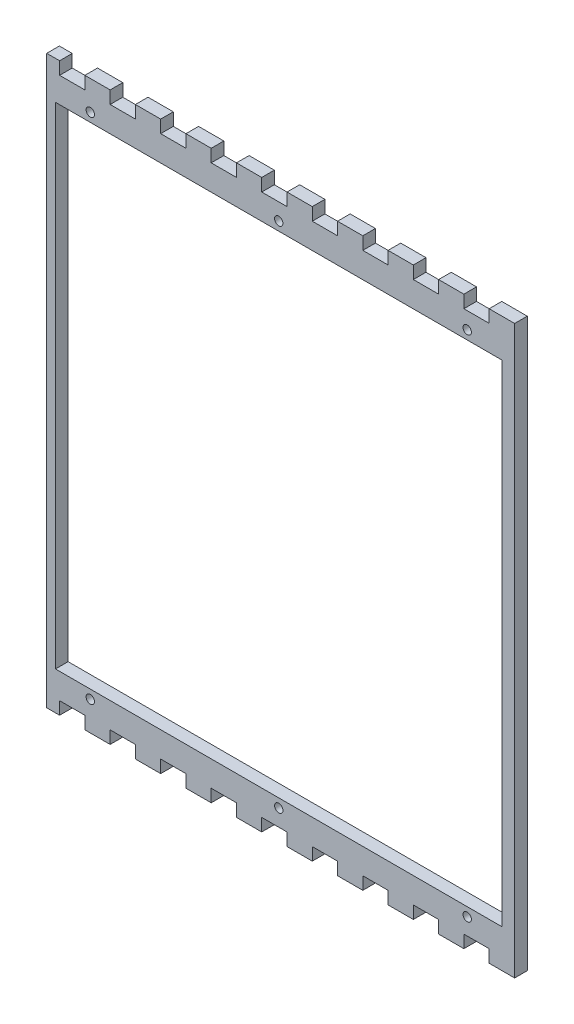
SolidWorks part; units mm, degrees
ref_plane "Front Plane" through (0, 0, 0) normal (0, 0, 1) x (1, 0, 0)
ref_plane "Top Plane" through (0, 0, 0) normal (0, 1, 0) x (1, 0, 0)
ref_plane "Right Plane" through (0, 0, 0) normal (1, 0, 0) x (0, 0, -1)
sketch "Model" plane through (0, 0, 0) normal (0, 0, 1) x (1, 0, 0)
  line L667 (1024.0797, 23.2006) -> (1029.904, 23.2006)
  line L668 (1029.904, 23.2006) -> (1029.904, 28.9154)
  line L669 (1029.904, 28.9154) -> (1041.334, 28.9154)
  line L670 (1041.334, 28.9154) -> (1041.334, 23.2006)
  line L671 (1041.334, 23.2006) -> (1052.764, 23.2006)
  line L672 (1052.764, 23.2006) -> (1052.764, 28.9154)
  line L673 (1052.764, 28.9154) -> (1064.194, 28.9154)
  line L674 (1064.194, 28.9154) -> (1064.194, 23.2006)
  line L675 (1064.194, 23.2006) -> (1075.624, 23.2006)
  line L676 (1075.624, 23.2006) -> (1075.624, 28.9154)
  line L677 (1075.624, 28.9154) -> (1087.054, 28.9154)
  line L678 (1087.054, 28.9154) -> (1087.054, 23.2006)
  line L679 (1087.054, 23.2006) -> (1098.484, 23.2006)
  line L680 (1098.484, 23.2006) -> (1098.484, 28.9154)
  line L681 (1098.484, 28.9154) -> (1109.914, 28.9154)
  line L682 (1109.914, 28.9154) -> (1109.914, 23.2006)
  line L683 (1109.914, 23.2006) -> (1121.344, 23.2006)
  line L684 (1121.344, 23.2006) -> (1121.344, 28.9154)
  line L685 (1121.344, 28.9154) -> (1132.774, 28.9154)
  line L686 (1132.774, 28.9154) -> (1132.774, 23.2006)
  line L687 (1132.774, 23.2006) -> (1144.204, 23.2006)
  line L688 (1144.204, 23.2006) -> (1144.204, 28.9154)
  line L689 (1144.204, 28.9154) -> (1155.634, 28.9154)
  line L690 (1155.634, 28.9154) -> (1155.634, 23.2006)
  line L691 (1155.634, 23.2006) -> (1167.064, 23.2006)
  line L692 (1167.064, 23.2006) -> (1167.064, 28.9154)
  line L693 (1167.064, 28.9154) -> (1178.494, 28.9154)
  line L694 (1178.494, 28.9154) -> (1178.494, 23.2006)
  line L695 (1178.494, 23.2006) -> (1189.924, 23.2006)
  line L696 (1189.924, 23.2006) -> (1189.924, 28.9154)
  line L697 (1189.924, 28.9154) -> (1201.354, 28.9154)
  line L698 (1201.354, 28.9154) -> (1201.354, 23.2006)
  line L699 (1201.354, 23.2006) -> (1212.784, 23.2006)
  line L700 (1212.784, 23.2006) -> (1212.784, 28.9154)
  line L701 (1212.784, 28.9154) -> (1224.214, 28.9154)
  line L702 (1224.214, 28.9154) -> (1224.214, 23.2006)
  line L703 (1224.214, 23.2006) -> (1235.7532, 23.2006)
  line L704 (1235.7532, 23.2006) -> (1235.7532, 279.6311)
  line L705 (1235.7532, 279.6311) -> (1224.214, 279.6311)
  line L706 (1224.214, 279.6311) -> (1224.214, 273.9161)
  line L707 (1224.214, 273.9161) -> (1212.784, 273.9161)
  line L708 (1212.784, 273.9161) -> (1212.784, 279.6311)
  line L709 (1212.784, 279.6311) -> (1201.354, 279.6311)
  line L710 (1201.354, 279.6311) -> (1201.354, 273.9161)
  line L711 (1201.354, 273.9161) -> (1189.924, 273.9161)
  line L712 (1189.924, 273.9161) -> (1189.924, 279.6311)
  line L713 (1189.924, 279.6311) -> (1178.494, 279.6311)
  line L714 (1178.494, 279.6311) -> (1178.494, 273.9161)
  line L715 (1178.494, 273.9161) -> (1167.064, 273.9161)
  line L716 (1167.064, 273.9161) -> (1167.064, 279.6311)
  line L717 (1167.064, 279.6311) -> (1155.634, 279.6311)
  line L718 (1155.634, 279.6311) -> (1155.634, 273.9161)
  line L719 (1155.634, 273.9161) -> (1144.204, 273.9161)
  line L720 (1144.204, 273.9161) -> (1144.204, 279.6311)
  line L721 (1144.204, 279.6311) -> (1132.774, 279.6311)
  line L722 (1132.774, 279.6311) -> (1132.774, 273.9161)
  line L723 (1132.774, 273.9161) -> (1121.344, 273.9161)
  line L724 (1121.344, 273.9161) -> (1121.344, 279.6311)
  line L725 (1121.344, 279.6311) -> (1109.914, 279.6311)
  line L726 (1109.914, 279.6311) -> (1109.914, 273.9161)
  line L727 (1109.914, 273.9161) -> (1098.484, 273.9161)
  line L728 (1098.484, 273.9161) -> (1098.484, 279.6311)
  line L729 (1098.484, 279.6311) -> (1087.054, 279.6311)
  line L730 (1087.054, 279.6311) -> (1087.054, 273.9161)
  line L731 (1087.054, 273.9161) -> (1075.624, 273.9161)
  line L732 (1075.624, 273.9161) -> (1075.624, 279.6311)
  line L733 (1075.624, 279.6311) -> (1064.194, 279.6311)
  line L734 (1064.194, 279.6311) -> (1064.194, 273.9161)
  line L735 (1064.194, 273.9161) -> (1052.764, 273.9161)
  line L736 (1052.764, 273.9161) -> (1052.764, 279.6311)
  line L737 (1052.764, 279.6311) -> (1041.334, 279.6311)
  line L738 (1041.334, 279.6311) -> (1041.334, 273.9161)
  line L739 (1041.334, 273.9161) -> (1029.904, 273.9161)
  line L740 (1029.904, 273.9161) -> (1029.904, 279.6311)
  line L741 (1029.904, 279.6311) -> (1024.0797, 279.6311)
  line L742 (1024.0797, 279.6311) -> (1024.0797, 23.2006)
extrude "Boss-Extrude1" add sketch "Model" along normal blind 5.715
sketch "Sketch1" plane through (0, 0, 0) normal (0, 0, -1) x (-1, 0, 0)
  line L22 (-1230.0382, 40.4157) -> (-1028.0382, 40.4157)
  line L23 (-1028.0382, 40.4157) -> (-1028.0382, 262.4157)
  line L24 (-1230.0382, 262.4157) -> (-1230.0382, 40.4157)
  line L25 (-1028.0382, 262.4157) -> (-1230.0382, 262.4157)
  line L26 (-1230.0382, 40.4157) -> (-1028.0382, 40.4157)
  line L27 (-1028.0382, 40.4157) -> (-1028.0382, 262.4157)
  line L28 (-1230.0382, 262.4157) -> (-1230.0382, 40.4157)
  line L29 (-1028.0382, 262.4157) -> (-1230.0382, 262.4157)
  dimension "D1" = 0.5
extrude "Cut-Extrude1" cut sketch "Sketch1" against normal through all
hole_wizard "CSK for #6 Flat Head Socket Cap Screw1" positions "Sketch4" profile "Sketch5" countersink size "#6" standard "ANSI Inch"
sketch "Sketch4" plane through (1095.0385, 151.4157, 0) normal (0, 0, -1) x (-1, 0, 0)
  point P0 (-119.2497, 115)
  point P3 (-33.9997, 115)
  point P6 (51.2503, 115)
  point P9 (51.2503, -115)
  point P12 (-33.9997, -115)
  point P15 (-119.2497, -115)
sketch "Sketch5" plane through (1214.2882, 266.4158, 0) normal (1, 0, 0) x (0, 1, 0)
  line L0 (0, 0) -> (0, 21.1408)
  line L1 (0, 21.1408) -> (1.8986, 20)
  line L2 (1.8986, 20) -> (1.8986, 2.301)
  line L3 (1.8986, 2.301) -> (3.8989, 0)
  line L4 (3.8989, 0) -> (0, 0)
  line L5 (-1.8986, 2.301) -> (-3.8989, 0) construction
  line L6 (0, 21.1408) -> (-1.8987, 20) construction
  line L7 (0, -6.35) -> (0, 107.95) construction
  dimension "Hole Dia." = 3.7973
  dimension "Hole Depth" = 20
  dimension "Near C'Sink Dia." = 7.7978
  dimension "Near C'Sink Angle" = 82
  dimension "Drill Angle" = 118
